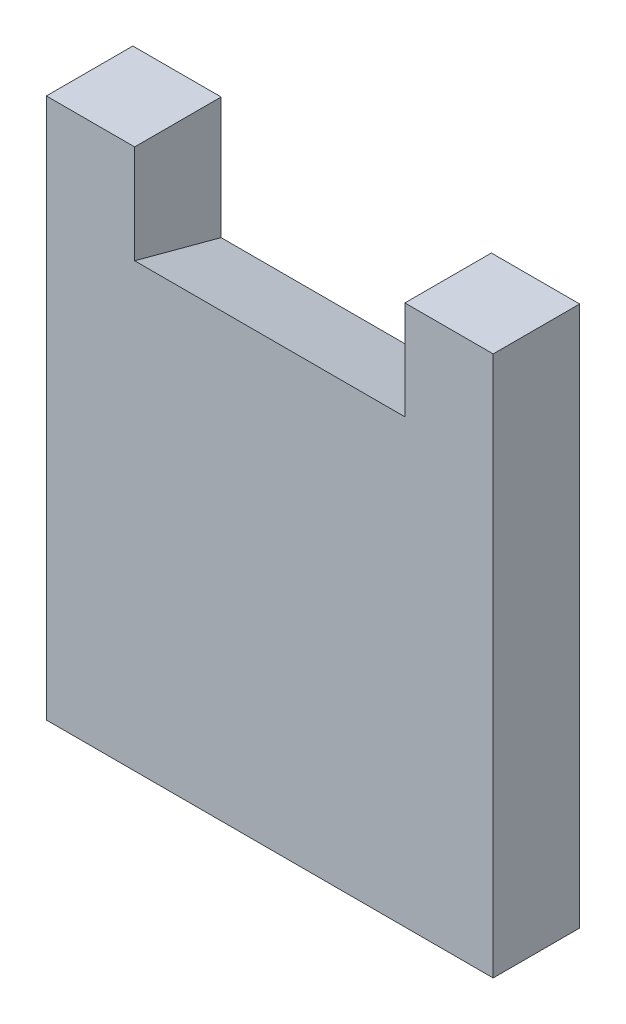
SolidWorks part; units mm, degrees
ref_plane "前视基准面" through (0, 0, 0) normal (0, 0, 1) x (1, 0, 0)
ref_plane "上视基准面" through (0, 0, 0) normal (0, 1, 0) x (1, 0, 0)
ref_plane "右视基准面" through (0, 0, 0) normal (1, 0, 0) x (0, 0, -1)
sketch "草图1" plane through (0, 0, 0) normal (0, 0, 1) x (1, 0, 0)
  line L1 (0, 0) -> (49.6, 0)
  line L2 (0, 0) -> (0, -60)
  line L3 (0, -60) -> (49.6, -60)
  line L4 (49.6, 0) -> (49.6, -60)
  line L5 (9.8, 0) -> (39.8, 0)
  line L6 (9.8, 0) -> (9.8, -10.95)
  line L7 (9.8, -10.95) -> (39.8, -10.95)
  line L8 (39.8, 0) -> (39.8, -10.95)
  point P9 (24.8, 0)
  dimension "D1" = 60
  dimension "D2" = 49.6
  dimension "D3" = 30
  dimension "D4" = 49.05
extrude "凸台-拉伸1" add sketch "草图1" along normal blind 9.6 contours L1 L8 L7 L6 L2 L3 L4
draft "拔模5" type of draft neutral plane draft angle 15 faces to draft 1 face at (24.8, -10.95, 4.8) neutral plane through (0, 0, 9.6) neutral plane normal (0, 0, 1) reverse direction yes parameters "D1"=15
